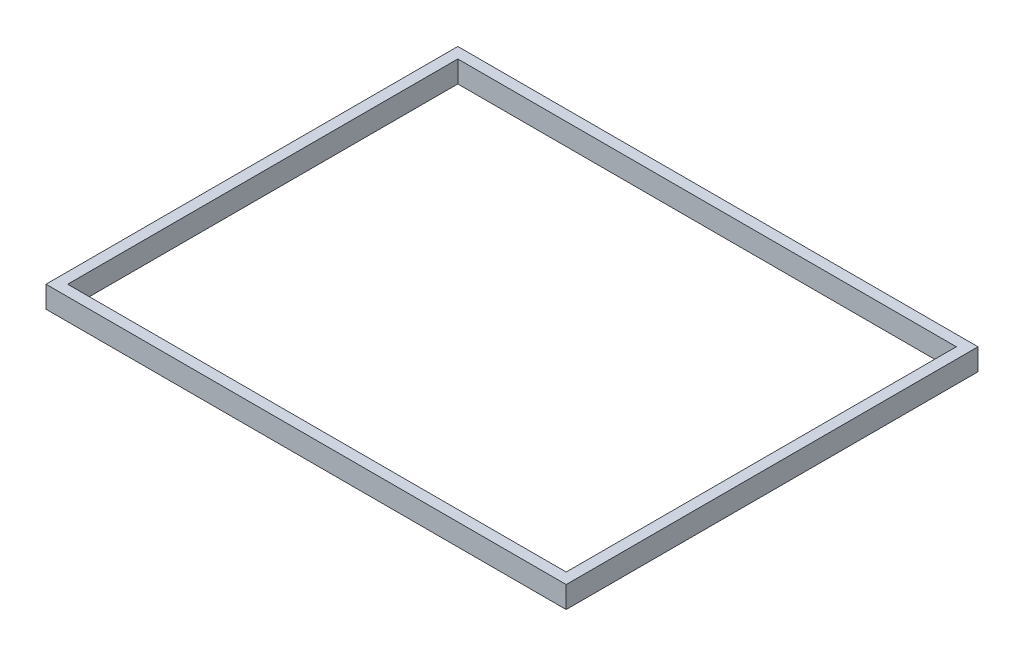
SolidWorks part; units mm, degrees
ref_plane "Front Plane" through (0, 0, 0) normal (0, 0, 1) x (1, 0, 0)
ref_plane "Top Plane" through (0, 0, 0) normal (0, 1, 0) x (1, 0, 0)
ref_plane "Right Plane" through (0, 0, 0) normal (1, 0, 0) x (0, 0, -1)
sketch "Sketch1" plane through (0, 0, 0) normal (0, 1, 0) x (1, 0, 0)
  line L0 (-230, 180) -> (230, 180)
  line L1 (-240, -190) -> (240, -190)
  line L2 (-240, -190) -> (-240, 190)
  line L3 (-240, 190) -> (240, 190)
  line L4 (240, -190) -> (240, 190)
  line L5 (-240, -190) -> (240, 190) construction
  line L6 (-240, 190) -> (240, -190) construction
  line L7 (230, -180) -> (230, 180)
  line L8 (-230, -180) -> (230, -180)
  line L9 (-230, -180) -> (-230, 180)
  point P0 (0, 0)
  dimension "D1" = 480
  dimension "D2" = 380
  dimension "D3" = 10
extrude "Boss-Extrude1" add sketch "Sketch1" along normal blind 20
